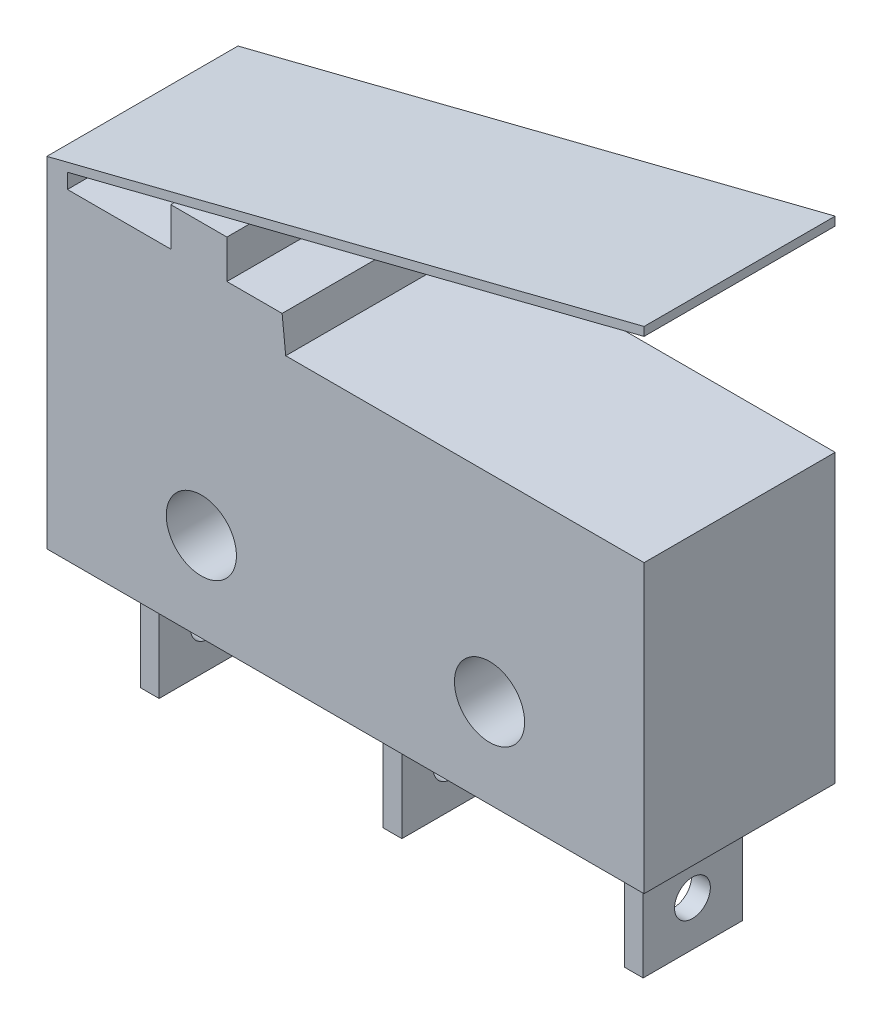
SolidWorks part; units mm, degrees
ref_plane "Plan de face" through (0, 0, 0) normal (0, 0, 1) x (1, 0, 0)
ref_plane "Plan de dessus" through (0, 0, 0) normal (0, 1, 0) x (1, 0, 0)
ref_plane "Plan de droite" through (0, 0, 0) normal (1, 0, 0) x (0, 0, -1)
sketch "Esquisse1" plane through (0, 0, 0) normal (0, 0, 1) x (1, 0, 0)
  line L1 (1.3618, 21.0416) -> (21.3618, 21.0416)
  line L2 (1.3618, 21.0416) -> (1.3618, 30.6416)
  line L3 (1.3618, 30.6416) -> (21.3618, 30.6416)
  line L4 (21.3618, 21.0416) -> (21.3618, 30.6416)
  dimension "D1" = 20
  dimension "D2" = 9.6
extrude "Boss.-Extru.1" add sketch "Esquisse1" along normal blind 6.4
sketch "Esquisse2" plane through (0, 0, 6.4) normal (0, 0, 1) x (1, 0, 0)
  line L0 (1.3618, 21.0416) -> (21.3618, 21.0416) construction
  line L1 (21.3618, 21.0416) -> (21.3618, 30.6416) construction
  line L2 (11.3618, 30.6416) -> (11.3618, 21.0416) construction
  line L3 (21.3618, 30.6416) -> (1.3618, 30.6416) construction
  circle A0 centre (16.1868, 24.0166) radius 1.175
  circle A1 centre (6.5368, 24.0166) radius 1.175
  dimension "D1" = 2.35
  dimension "D2" = 2.975
  dimension "D3" = 5.175
extrude "Enlèv. mat.-Extru.1" cut sketch "Esquisse2" against normal blind 6.4
sketch "Esquisse4" plane through (0, 0, 6.4) normal (0, 0, 1) x (1, 0, 0)
  line L0 (1.3618, 32.4247) -> (1.3618, 30.6416)
  line L1 (2.0523, 31.8097) -> (5.5123, 31.8097)
  line L2 (9.2412, 31.8097) -> (9.3618, 30.6416)
  line L3 (21.3618, 30.6416) -> (1.3618, 30.6416) construction
  line L4 (5.5123, 31.8097) -> (5.5123, 33.0997)
  line L5 (5.5123, 33.0997) -> (7.3923, 33.0997)
  line L6 (7.3923, 33.0997) -> (7.3923, 31.8097)
  line L7 (9.3618, 30.6416) -> (1.3618, 30.6416)
  line L8 (7.3923, 31.8097) -> (9.2412, 31.8097)
  line L9 (2.0523, 32.3097) -> (2.0523, 31.8097)
  line L11 (1.3618, 32.4247) -> (21.3618, 37.4916)
  line L12 (21.3618, 37.4916) -> (21.3618, 37.2016)
  line L13 (21.3618, 37.2016) -> (2.0523, 32.3097)
  line L14 (21.3618, 30.6416) -> (21.3618, 44.3753) construction
  dimension "D1" = 0.29
  dimension "D3" = 1.29
  dimension "D5" = 0.7
  dimension "D6" = 20
  dimension "D7" = 1.88
  dimension "D8" = 3.46
  dimension "D9" = 0.5
  dimension "D10" = 8
  dimension "D11" = 1.1681
extrude "Boss.-Extru.66" add sketch "Esquisse4" against normal blind 6.4
ref_plane "Plan1" through (0, 0, 6.4) normal (0, 0, 1) x (1, 0, 0)
sketch "Esquisse5" plane through (0, 21.0416, 0) normal (0, -1, 0) x (1, 0, 0)
  line L0 (1.3618, 6.4) -> (1.3618, 0) construction
  line L1 (2.9418, 1.52) -> (3.5718, 1.52)
  line L2 (2.9418, 1.52) -> (2.9418, 4.85)
  line L3 (2.9418, 4.85) -> (3.5718, 4.85)
  line L4 (3.5718, 1.52) -> (3.5718, 4.85)
  line L5 (11.0718, 1.52) -> (11.7018, 1.52)
  line L6 (11.0718, 1.52) -> (11.0718, 4.85)
  line L7 (11.0718, 4.85) -> (11.7018, 4.85)
  line L8 (11.7018, 1.52) -> (11.7018, 4.85)
  line L9 (19.1518, 1.52) -> (19.7818, 1.52)
  line L10 (19.1518, 1.52) -> (19.1518, 4.85)
  line L11 (19.1518, 4.85) -> (19.7818, 4.85)
  line L12 (19.7818, 1.52) -> (19.7818, 4.85)
  line L13 (21.3618, 6.4) -> (21.3618, 0) construction
  line L14 (9.2999, 6.4) -> (-9.2999, 6.4) construction
  dimension "D1" = 3.33
  dimension "D2" = 3.33
  dimension "D3" = 3.33
  dimension "D4" = 0.63
  dimension "D5" = 0.63
  dimension "D6" = 0.63
  dimension "D7" = 1.58
  dimension "D8" = 1.58
  dimension "D9" = 7.5
  dimension "D10" = 1.55
  dimension "D11" = 1.55
extrude "Boss.-Extru.67" add sketch "Esquisse5" along normal blind 4.01
sketch "Esquisse6" plane through (2.9418, 0, 0) normal (-1, 0, 0) x (0, 0, 1)
  line L0 (4.85, 17.0316) -> (1.52, 17.0316) construction
  line L1 (4.85, 17.0316) -> (4.85, 21.0416) construction
  circle A0 centre (3.2, 18.5316) radius 0.6
  dimension "D1" = 1.2
  dimension "D2" = 1.5
  dimension "D3" = 1.65
extrude "Enlèv. mat.-Extru.2" cut sketch "Esquisse6" against normal blind 19.01
